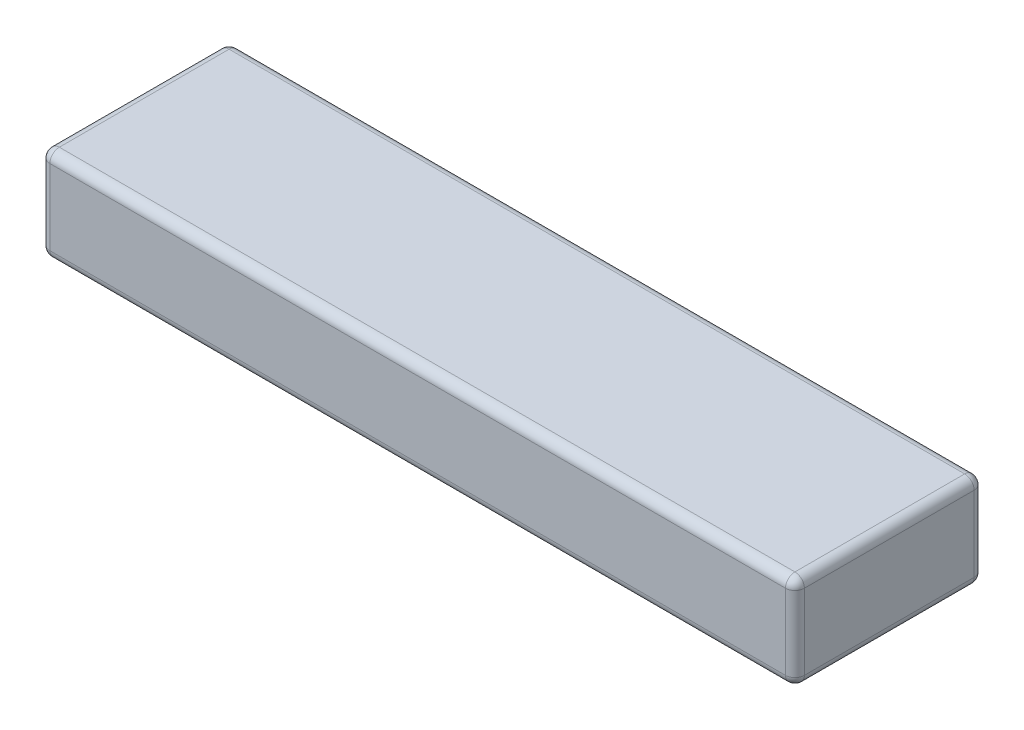
SolidWorks part; units mm, degrees
material "Alloy Steel"
ref_plane "Front Plane" through (0, 0, 0) normal (0, 0, 1) x (1, 0, 0)
ref_plane "Top Plane" through (0, 0, 0) normal (0, 1, 0) x (1, 0, 0)
ref_plane "Right Plane" through (0, 0, 0) normal (1, 0, 0) x (0, 0, -1)
sketch "Sketch1" plane through (0, 0, 0) normal (0, 1, 0) x (1, 0, 0)
  line L1 (-20, -5) -> (20, -5)
  line L2 (-20, -5) -> (-20, 5)
  line L3 (-20, 5) -> (20, 5)
  line L4 (20, -5) -> (20, 5)
  line L5 (-20, -5) -> (20, 5) construction
  line L6 (-20, 5) -> (20, -5) construction
  point P0 (0, 0)
  dimension "D1" = 10
  dimension "D2" = 40
extrude "Boss-Extrude1" add sketch "Sketch1" along normal blind 5
fillet "Fillet1" radius 0.5 12 edges at (-20, 0, 0) (-20, 2.5, -5) (0, 0, -5) (-20, 5, 0) (0, 5, -5) (20, 5, 0) (20, 2.5, -5) (20, 0, 0) (-20, 2.5, 5) (0, 5, 5) (20, 2.5, 5) (0, 0, 5)
